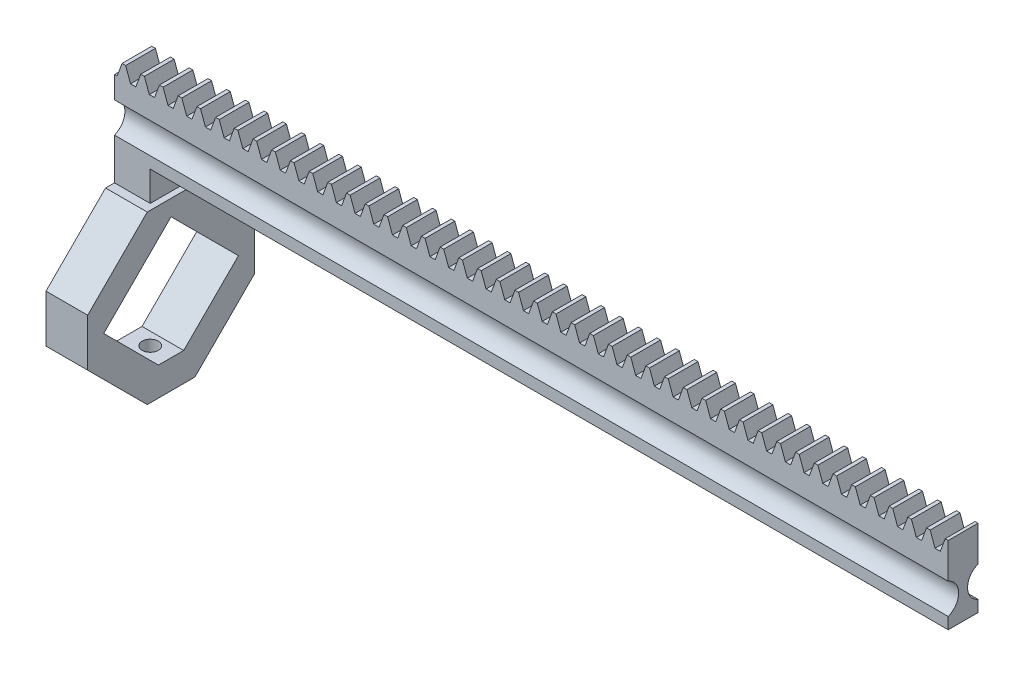
SolidWorks part; units mm, degrees
extrude "Blank" add sketch "BlankSke" against normal blind 5
sketch "BlankSke" plane through (0, 0, 0) normal (0, 0, 1) x (1, 0, 0)
  line L1 (0, 0) -> (140, 0)
  line L2 (0, 0) -> (0, 13)
  line L3 (0, 13) -> (140, 13)
  line L4 (140, 0) -> (140, 13)
  dimension "Length" = 140
  dimension "Blank_height" = 13
ref_plane "Plane1" through (0, 0, 0) normal (0, 0, 1) x (1, 0, 0)
ref_plane "Plane2" through (0, 0, 0) normal (0, 1, 0) x (1, 0, 0)
ref_plane "Plane3" through (0, 0, 0) normal (1, 0, 0) x (0, 0, -1)
sketch "HoldingSke" plane through (0, 0, 0) normal (0, 1, 0) x (1, 0, 0)
  line L0 (0, 0) -> (0.1392, 0.9903)
  line L1 (-15, 0) -> (100, 0) construction
  line L2 (0, 0) -> (-2.1039, 2.3779)
  line L3 (0, 0) -> (-11.863, 4.5341)
  line L4 (0, 0) -> (5.9991, 6.2122)
  line L5 (0, 0) -> (-23.7986, -8.8762)
  line L6 (0, 0) -> (-10.5278, -7.1032)
  line L9 (-71.009, 38.7566) -> (60.548, 86.6394)
  line L10 (-76.2, 3.3779) -> (-64.2, 3.3779)
  line L11 (0, 0) -> (-5, 0)
  line L12 (-76.2, 101.6) -> (-76.162, 101.6)
  line L13 (24.9733, 27.94) -> (52.9518, 28.4284)
  line L14 (24.9733, 27.94) -> (24.9743, 27.94)
  line L15 (24.9733, 27.94) -> (100.4006, 29.5858)
  circle A0 centre (0, 0) radius 19.05
  circle A1 centre (0, 0) radius 6
  circle A2 centre (0, 0) radius 12.7
  dimension "MPH" = 12
  dimension "Diameter" = 38.1
  dimension "Num_teeth" = 46
  dimension "Pitch" = 1
  dimension "Show_teeth" = 998
  dimension "Thickness" = 12.7
  dimension "Ap" = 20
  dimension "Pitch_height" = 12
  dimension "Width" = 5
  dimension "Backlash" = 0.038
  dimension "Addendum_fac" = 1
  dimension "Dedendum_fac" = 1.25
  dimension "Clearance_fac" = 0.25
  dimension "Dedendum_add" = 0.001
  dimension "Length" = 140
  dimension "Module" = 1
sketch "TooCutSkeIll" plane through (0, 0, 0) normal (0, 0, 1) x (1, 0, 0)
  line L0 (-1.2538, 12.9737) -> (-0.5045, 10.9152)
  line L1 (-0.2687, 10.75) -> (0.2687, 10.75)
  line L2 (0.5045, 10.9152) -> (1.2538, 12.9737)
  line L3 (140, 13) -> (0, 13) construction
  line L4 (0, 0) -> (0, 64.897) construction
  line L5 (-13.208, 12) -> (12.954, 12) construction
  line L6 (0, 0) -> (140, 0) construction
  line L7 (0.8994, 12) -> (0.8994, 48.7463) construction
  line L8 (-0.8994, 12) -> (-0.8994, 48.7463) construction
  line L9 (1.2914, 13) -> (1.2914, 13.0254)
  line L10 (-1.2914, 13) -> (-1.2914, 13.0254)
  line L11 (-1.2914, 13.0254) -> (1.2914, 13.0254)
  arc A0 (0.2687, 10.75) -> (0.5045, 10.9152) centre (0.2687, 11.001) ccw
  arc A1 (-0.5045, 10.9152) -> (-0.2687, 10.75) centre (-0.2687, 11.001) ccw
  arc A2 (1.2914, 13) -> (1.2538, 12.9737) centre (1.2914, 12.96) ccw
  arc A3 (-1.2538, 12.9737) -> (-1.2914, 13) centre (-1.2914, 12.96) ccw
  dimension "Pitch_height" = 12
  dimension "Addendum_plus" = 1.0254
  dimension "Pressure_angle" = 20
  dimension "Gap_width" = 1.7988
  dimension "Dedendum" = 1.25
extrude "ToothCutIll" [suppressed] cut sketch "TooCutSkeIll" against normal through all
sketch "TooCutSkeSim" plane through (0, 0, 0) normal (0, 0, 1) x (1, 0, 0)
  line L0 (0.4444, 10.75) -> (-0.4444, 10.75)
  line L1 (1.2726, 13.0254) -> (0.4444, 10.75)
  line L2 (0, 17.4625) -> (0, 53.467) construction
  line L3 (1.2726, 13.0254) -> (-1.2726, 13.0254)
  line L6 (-1.2726, 13.0254) -> (-0.4444, 10.75)
  line L9 (-0.8994, 12) -> (0.8994, 12) construction
  line L10 (0, 0) -> (140, 0) construction
  line L11 (0.8994, 12) -> (0.8994, 53.467) construction
  line L12 (-0.8994, 12) -> (-0.8994, 53.467) construction
  dimension "Pitch_height" = 12
  dimension "Addendum_plus" = 1.0254
  dimension "Pressure_angle" = 20
  dimension "Gap_width" = 1.7988
  dimension "Dedendum" = 1.25
extrude "ToothCutSim" cut sketch "TooCutSkeSim" against normal through all
pattern_linear "TeethCuts" count 45 spacing 3.1416 along (1, 0, 0) of "ToothCutIll", "ToothCutSim"
sketch "Sketch1" plane through (0, 0, 0) normal (1, 0, 0) x (0, 0, -1)
  line L1 (2.5, 0) -> (2.5, 6.3459) construction
  line L2 (5, 0) -> (0, 0) construction
  circle A0 centre (6, 4.5) radius 2.75
  circle A1 centre (-1, 4.5) radius 2.75
  dimension "D1" = 4.5
  dimension "5." = 5.5
  dimension "D3" = 3.5
extrude "Cut-Extrude2" cut sketch "Sketch1" against normal blind 10 and the other way through all contours A0 | A1
sketch "Sketch2" plane through (0, 0, 0) normal (0, 0, 1) x (1, 0, 0)
  line L1 (0, 10.75) -> (6, 10.75)
  line L2 (0, 10.75) -> (0, 15.75)
  line L3 (0, 15.75) -> (6, 15.75)
  line L4 (6, 10.75) -> (6, 15.75)
  dimension "D1" = 5
  dimension "D2" = 6
sketch "Sketch15" plane through (0, 0, 0) normal (0, -1, 0) x (1, 0, 0)
  line L0 (0, -5) -> (140, -5) construction
  line L1 (0, 0) -> (6, 0)
  line L2 (0, 0) -> (0, -5)
  line L3 (0, -5) -> (6, -5)
  line L4 (6, 0) -> (6, -5)
  dimension "D1" = 6
  dimension "D2" = 5
extrude "Boss-Extrude4" add sketch "Sketch15" along normal blind 5
sketch "Sketch16" plane through (0, 0, 0) normal (-1, 0, 0) x (0, 0, 1)
  line L0 (0, -5) -> (-5, -5) construction
  line L1 (-16.5, -33) -> (11.5, -33)
  line L2 (-16.5, -33) -> (-16.5, -5)
  line L3 (-16.5, -5) -> (11.5, -5)
  line L4 (11.5, -33) -> (11.5, -5)
  line L5 (-16.5, -33) -> (11.5, -5) construction
  line L6 (-16.5, -5) -> (11.5, -33) construction
  line L7 (-5, 1.9383) -> (-5, -5) construction
  line L9 (0, 1.9383) -> (0, -5) construction
  point P0 (-2.5, -19)
  dimension "D1" = 28
  dimension "D2" = 28
  dimension "D3" = 28
  dimension "D4" = 11.5
  dimension "D5" = 11.5
extrude "Boss-Extrude5" add sketch "Sketch16" against normal blind 7
sketch "Sketch17" plane through (0, 0, 0) normal (-1, 0, 0) x (0, 0, 1)
  line L0 (-16.5, -19) -> (11.5, -19) construction
  line L1 (-16.5, -5) -> (-16.5, -33) construction
  line L2 (11.5, -33) -> (11.5, -5) construction
  line L3 (-2.5, -33) -> (-2.5, -4.8171) construction
  line L4 (-16.5, -33) -> (11.5, -33) construction
  line L5 (-13.8137, -19) -> (-2.5, -7.6863)
  line L6 (-2.5, -7.6863) -> (8.8137, -19)
  line L7 (8.8137, -19) -> (-2.5, -30.3137)
  line L8 (-2.5, -30.3137) -> (-13.8137, -19)
  dimension "D1" = 16
  dimension "D2" = 16
extrude "Cut-Extrude6" cut sketch "Sketch17" against normal blind 10
chamfer "Chamfer4" distance 3 angle 45 1 edges at (3.5, -30.3137, -2.5)
chamfer "Chamfer5" distance 10 angle 45 4 edges at (3.5, -33, -16.5) (3.5, -33, 11.5) (3.5, -5, 11.5) (3.5, -5, -16.5)
sketch "Sketch18" plane through (0, -33, 0) normal (0, -1, 0) x (1, 0, 0)
  line L0 (0, -2.5) -> (7, -2.5) construction
  line L1 (0, -6.5) -> (0, 1.5) construction
  line L2 (7, -6.5) -> (7, 1.5) construction
  line L3 (3.5, 1.5) -> (3.5, -6.5) construction
  line L4 (7, 1.5) -> (0, 1.5) construction
  line L5 (0, -6.5) -> (7, -6.5) construction
  circle A0 centre (3.5, -2.5) radius 1.35
  dimension "D1" = 2.7
extrude "Cut-Extrude7" cut sketch "Sketch18" against normal blind 10
sketch "Sketch19" plane through (0, 0, 0) normal (0, -1, 0) x (1, 0, 0)
  line L1 (140, -5) -> (6, -5)
  line L2 (140, -5) -> (140, 0)
  line L3 (140, 0) -> (6, 0)
  line L4 (6, -5) -> (6, 0)
equation "' \"Module@HoldingSke\" = 6.35"
equation "' \"Num_teeth@HoldingSke\" = 12"
equation "' \"Ap@HoldingSke\" =  20"
equation "' \"Ap@HoldingSke\" = 20"
equation "' \"Width@HoldingSke\" = 0.25 * 25.4"
equation "' \"Show_teeth@HoldingSke\" = 500"
equation "' \"Backlash@HoldingSke\" = 0.009 * 25.4"
equation "' \"Addendum_fac@HoldingSke\" = 1.0"
equation "' \"Dedendum_fac@HoldingSke\" = 1.25"
equation "' \"Dedendum_add@HoldingSke\" = 0.00005 * 25.4"
equation "' \"Clearance_fac@HoldingSke\" = 0.25"
equation "' \"Pitch_height@HoldingSke\" = 1 * 25.4"
equation "' \"Length@HoldingSke\" = 4.71 * 25.4"
equation "\"Pitch@HoldingSke\" = 1 / \"Module@HoldingSke\""
equation "\"MPH@HoldingSke\" = \"Dedendum_fac@HoldingSke\" / \"Pitch@HoldingSke\" + 2 * \"Dedendum_add@HoldingSke\" + 0.002 * 25.4"
equation "\"MPH@HoldingSke\" = ((sgn( \"MPH@HoldingSke\" - \"Pitch_height@HoldingSke\")+1)*( \"MPH@HoldingSke\" - \"Pitch_height@HoldingSke\"))/2 + \"Pitch_height@HoldingSke\""
equation "\"Blank_height@BlankSke\" = \"Pitch_height@HoldingSke\" + \"Addendum_fac@HoldingSke\"  / \"Pitch@HoldingSke\" "
equation "\"Length@BlankSke\" =  \"Length@HoldingSke\""
equation "\"Face_width@Blank\" = \"Width@HoldingSke\""
equation "\"Pressure_angle@TooCutSkeIll\" = \"Ap@HoldingSke\""
equation "\"Addendum_plus@TooCutSkeIll\" =  \"Addendum_fac@HoldingSke\"  / \"Pitch@HoldingSke\" + 0.001 *25.4"
equation "\"Dedendum@TooCutSkeIll\" = \"Dedendum_fac@HoldingSke\"  / \"Pitch@HoldingSke\""
equation "\"Pitch_height@TooCutSkeIll\" =  \"MPH@HoldingSke\""
equation "\"Gap_width@TooCutSkeIll\" = 3.14159265 / 2 / \"Pitch@HoldingSke\" + 6 * \"Backlash@HoldingSke\""
equation "\"Pressure_angle@TooCutSkeSim\" = \"Ap@HoldingSke\""
equation "\"Addendum_plus@TooCutSkeSim\" =  \"Addendum_fac@HoldingSke\"  / \"Pitch@HoldingSke\" + 0.001 * 25.4"
equation "\"Dedendum@TooCutSkeSim\" = \"Dedendum_fac@HoldingSke\"  / \"Pitch@HoldingSke\""
equation "\"Pitch_height@TooCutSkeSim\" =  \"MPH@HoldingSke\""
equation "\"Gap_width@TooCutSkeSim\" = 3.14159265 / 2 / \"Pitch@HoldingSke\" + 6 * \"Backlash@HoldingSke\""
equation "\"Root_fillet@TooCutSkeIll\" = \"Clearance_fac@HoldingSke\" / \"Pitch@HoldingSke\" + \"Dedendum_add@HoldingSke\""
equation "\"Break_rad@TooCutSkeIll\" = 0.02 / \"Pitch@HoldingSke\" * 2"
equation "\"Linear_pitch@TeethCuts\" = 3.14159265 / \"Pitch@HoldingSke\""
equation "\"Num_teeth@HoldingSke\" = int( ( \"Length@HoldingSke\" + 0 ) / (3.14159265 / \"Pitch@HoldingSke\")) + 0.9999  + 1"
equation " \"Num_teeth@TeethCuts\" = int( \"Show_teeth@HoldingSke\" ) + 1"
equation " \"Num_teeth@TeethCuts\" = ((sgn( \"Num_teeth@TeethCuts\" - \"Num_teeth@HoldingSke\" )-1)*( \"Num_teeth@TeethCuts\" - \"Num_teeth@HoldingSke\" ))/-2+ \"Num_teeth@HoldingSke\""
equation " \"Num_teeth@TeethCuts\" = ((sgn( \"Num_teeth@TeethCuts\" - 2.0)+1)*( \"Num_teeth@TeethCuts\" - 2.0))/2 +2.0"
